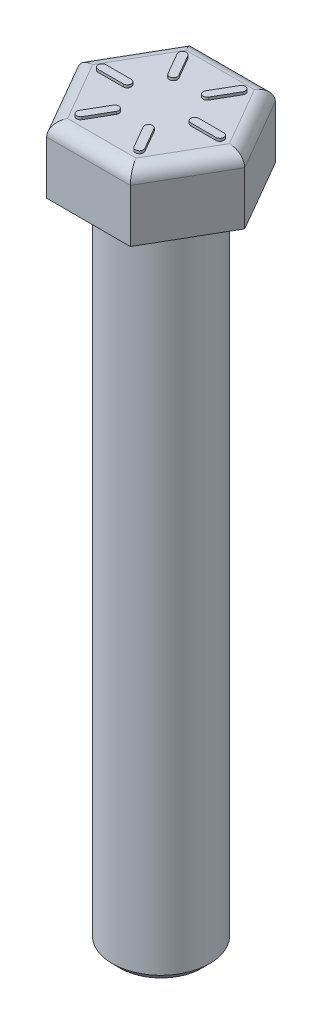
SolidWorks part; units mm, degrees
material "AISI 1045 Steel, cold drawn"
ref_plane "Front" through (0, 0, 0) normal (0, 0, 1) x (1, 0, 0)
ref_plane "Top" through (0, 0, 0) normal (0, 1, 0) x (1, 0, 0)
ref_plane "Right" through (0, 0, 0) normal (1, 0, 0) x (0, 0, -1)
sketch "Sketch1" plane through (0, 0, 0) normal (0, 1, 0) x (1, 0, 0)
  circle A0 centre (0, 0) radius 4.6609
  dimension "D1" = 9.3218
extrude "Boss-Extrude1" add sketch "Sketch1" against normal blind 63.5
cosmetic thread "Cosmetic Thread1" parameters "D1"=17.78, "D2"=6.2586
sketch "Sketch2" plane through (0, 0, 0) normal (0, 1, 0) x (1, 0, 0)
  line L1 (8.0289, 0) -> (4.0145, 6.9532)
  line L2 (4.0145, 6.9532) -> (-4.0145, 6.9532)
  line L3 (-4.0145, 6.9532) -> (-8.0289, 0)
  line L4 (-8.0289, 0) -> (-4.0145, -6.9532)
  line L5 (-4.0145, -6.9532) -> (4.0145, -6.9532)
  line L6 (4.0145, -6.9532) -> (8.0289, 0)
  circle A0 centre (0, 0) radius 6.9532 construction
  dimension "D1" = 13.9065
extrude "Boss-Extrude2" add sketch "Sketch2" along normal blind 6.35
fillet "Fillet1" radius 1.27
chamfer "Chamfer1" distance 0.762 angle 45
sketch "Sketch3" plane through (0, 6.35, 0) normal (0, 1, 0) x (1, 0, 0)
  line L0 (5.6515, 0) -> (3.2385, 0) construction
  line L1 (5.6515, -0.381) -> (3.2385, -0.381)
  line L2 (5.6515, 0.381) -> (3.2385, 0.381)
  line L3 (2.8258, 4.8943) -> (1.6193, 2.8046) construction
  line L4 (3.1557, 4.7038) -> (1.9492, 2.6141)
  line L5 (2.4958, 5.0848) -> (1.2893, 2.9951)
  line L6 (-2.8257, 4.8943) -> (-1.6192, 2.8046) construction
  line L7 (-2.4958, 5.0848) -> (-1.2893, 2.9951)
  line L8 (-3.1557, 4.7038) -> (-1.9492, 2.6141)
  line L9 (-5.6515, 0) -> (-3.2385, 0) construction
  line L10 (-5.6515, 0.381) -> (-3.2385, 0.381)
  line L11 (-5.6515, -0.381) -> (-3.2385, -0.381)
  line L12 (-2.8258, -4.8943) -> (-1.6193, -2.8046) construction
  line L13 (-3.1557, -4.7038) -> (-1.9492, -2.6141)
  line L14 (-2.4958, -5.0848) -> (-1.2893, -2.9951)
  line L15 (2.8258, -4.8943) -> (1.6192, -2.8046) construction
  line L16 (2.4958, -5.0848) -> (1.2893, -2.9951)
  line L17 (3.1557, -4.7038) -> (1.9492, -2.6141)
  arc A0 (5.6515, -0.381) -> (5.6515, 0.381) centre (5.6515, 0) ccw
  arc A1 (3.2385, 0.381) -> (3.2385, -0.381) centre (3.2385, 0) ccw
  circle A2 centre (0, 0) radius 2.8575 construction
  arc A3 (3.1557, 4.7038) -> (2.4958, 5.0848) centre (2.8258, 4.8943) ccw
  arc A4 (1.2893, 2.9951) -> (1.9492, 2.6141) centre (1.6193, 2.8046) ccw
  arc A5 (-2.4958, 5.0848) -> (-3.1557, 4.7038) centre (-2.8257, 4.8943) ccw
  arc A6 (-1.9492, 2.6141) -> (-1.2893, 2.9951) centre (-1.6192, 2.8046) ccw
  arc A7 (-5.6515, 0.381) -> (-5.6515, -0.381) centre (-5.6515, 0) ccw
  arc A8 (-3.2385, -0.381) -> (-3.2385, 0.381) centre (-3.2385, 0) ccw
  arc A9 (-3.1557, -4.7038) -> (-2.4958, -5.0848) centre (-2.8258, -4.8943) ccw
  arc A10 (-1.2893, -2.9951) -> (-1.9492, -2.6141) centre (-1.6193, -2.8046) ccw
  arc A11 (2.4958, -5.0848) -> (3.1557, -4.7038) centre (2.8258, -4.8943) ccw
  arc A12 (1.9492, -2.6141) -> (1.2893, -2.9951) centre (1.6192, -2.8046) ccw
  point P3 (4.445, 0)
  point P8 (6.0325, 0)
  point P9 (2.8575, 0)
  point P16 (2.2225, 3.8495)
  point P21 (3.0163, 5.2243)
  point P22 (1.4288, 2.4747)
  point P25 (-2.2225, 3.8495)
  point P30 (-3.0162, 5.2243)
  point P31 (-1.4287, 2.4747)
  point P34 (-4.445, 0)
  point P39 (-6.0325, 0)
  point P40 (-2.8575, 0)
  point P43 (-2.2225, -3.8495)
  point P48 (-3.0163, -5.2243)
  point P49 (-1.4288, -2.4747)
  point P52 (2.2225, -3.8495)
  point P57 (3.0163, -5.2243)
  point P58 (1.4288, -2.4747)
  point P59 (0, 0)
  dimension "D4" = 5.715
  dimension "D1" = 0.762
  dimension "D2" = 3.175
  dimension "D3" = 6.0325
  dimension "D5" = 6
extrude "Boss-Extrude3" add sketch "Sketch3" along normal blind 0.254
